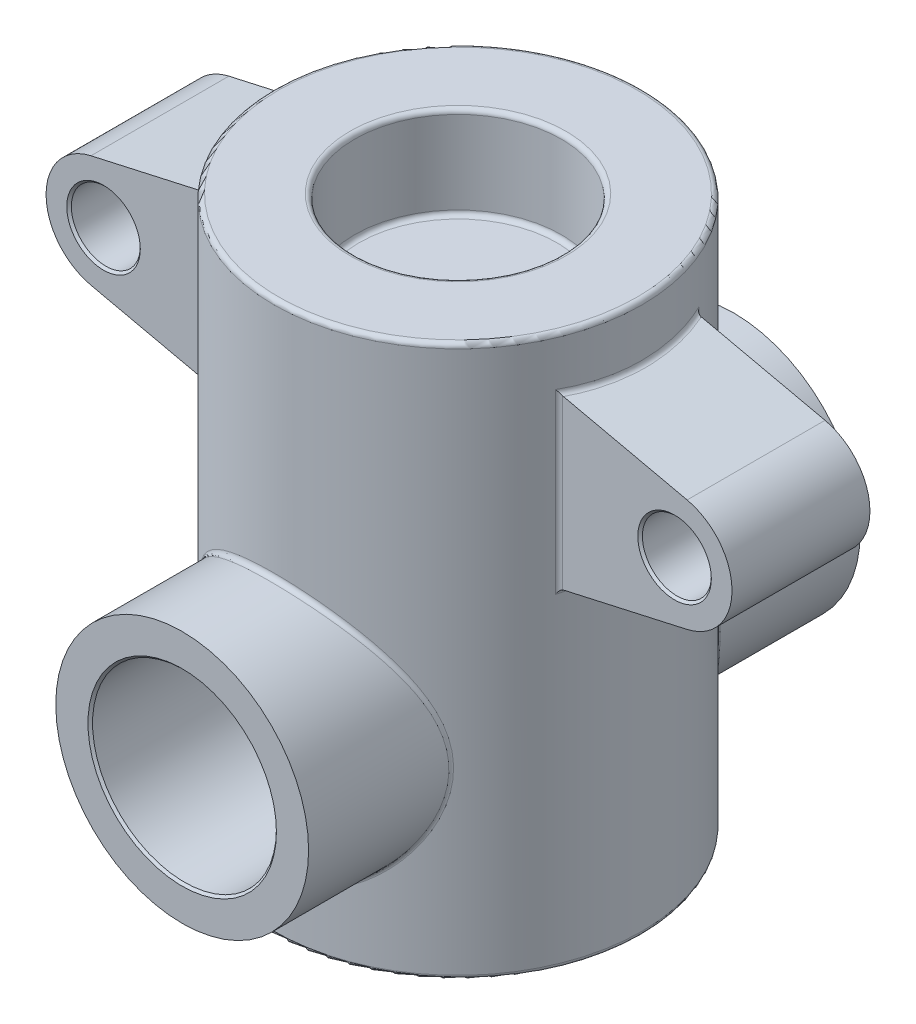
SolidWorks part; units mm, degrees
ref_plane "Front Plane" through (0, 0, 0) normal (0, 0, 1) x (1, 0, 0)
ref_plane "Top Plane" through (0, 0, 0) normal (0, 1, 0) x (1, 0, 0)
ref_plane "Right Plane" through (0, 0, 0) normal (1, 0, 0) x (0, 0, -1)
sketch "Sketch1" plane through (0, 0, 0) normal (0, 0, 1) x (1, 0, 0)
  line L1 (0, 0) -> (40, 0)
  line L2 (0, 0) -> (0, 120)
  line L3 (0, 120) -> (40, 120)
  line L4 (40, 0) -> (40, 120)
  dimension "D1" = 40
  dimension "D2" = 120
revolve "Revolve1" add sketch "Sketch1" angle 360 about L2
sketch "Sketch2" plane through (0, 0, 0) normal (0, 0, 1) x (1, 0, 0)
  line L0 (0, 134.1143) -> (0, -9.3046) construction
  line L1 (0, 120) -> (0, 0) construction
  line L2 (-59.8065, 90) -> (79.7582, 90) construction
  line L3 (40, 120) -> (-40, 120) construction
  line L4 (30, 110) -> (30, 70)
  line L5 (40, 0) -> (40, 120) construction
  line L6 (30, 110) -> (64.8412, 102.1979)
  line L7 (30, 70) -> (64.8412, 77.8021)
  arc A0 (64.8412, 77.8021) -> (64.8412, 102.1979) centre (62.1097, 90) ccw
  circle A1 centre (62.1097, 90) radius 7.5
  dimension "D1" = 25
  dimension "D7" = 15
  dimension "D2" = 30
  dimension "D3" = 0
  dimension "D4" = 10
  dimension "D5" = 40
  dimension "D6" = 20
extrude "Boss-Extrude1" add sketch "Sketch2" along normal mid plane 30
mirror "Mirror1" about plane through (0, 0, 0) normal (1, 0, 0) of "Boss-Extrude1"
sketch "Sketch3" plane through (0, 0, 0) normal (0, 0, 1) x (1, 0, 0)
  circle A0 centre (0, 40) radius 27.5
  dimension "D1" = 55
  dimension "D2" = 40
extrude "Boss-Extrude2" add sketch "Sketch3" along normal mid plane 120
sketch "Sketch4" plane through (0, 0, 0) normal (0, 0, 1) x (1, 0, 0)
  circle A0 centre (0, 40) radius 20
  dimension "D1" = 40
extrude "Cut-Extrude1" cut sketch "Sketch4" against normal mid plane 120
sketch "Sketch5" plane through (0, 120, 0) normal (0, 1, 0) x (1, 0, 0)
  circle A0 centre (0, 0) radius 22.5
  dimension "D1" = 45
extrude "Cut-Extrude2" cut sketch "Sketch5" against normal blind 20
fillet "Fillet1" radius 1 13 edges at (-22.5, 120, 0) (27.233, 43.8228, -29.2978) (27.233, 36.1772, 29.2978) (40, 72.2393, 0) (37.081, 90, -15) (40, 107.7607, 0) (37.081, 90, 15) (40, 0, 0) (40, 120, 0) (-40, 107.7607, 0) (-37.081, 90, -15) (-40, 72.2393, 0) (-37.081, 90, 15)
fillet "Fillet3" radius 1 1 edges at (-22.5, 100, 0)
chamfer "Chamfer1" distance 0.5 angle 45 6 edges at (20, 40, -60) (-69.6097, 90, 15) (-69.6097, 90, -15) (69.6097, 90, -15) (69.6097, 90, 15) (20, 40, 60)
